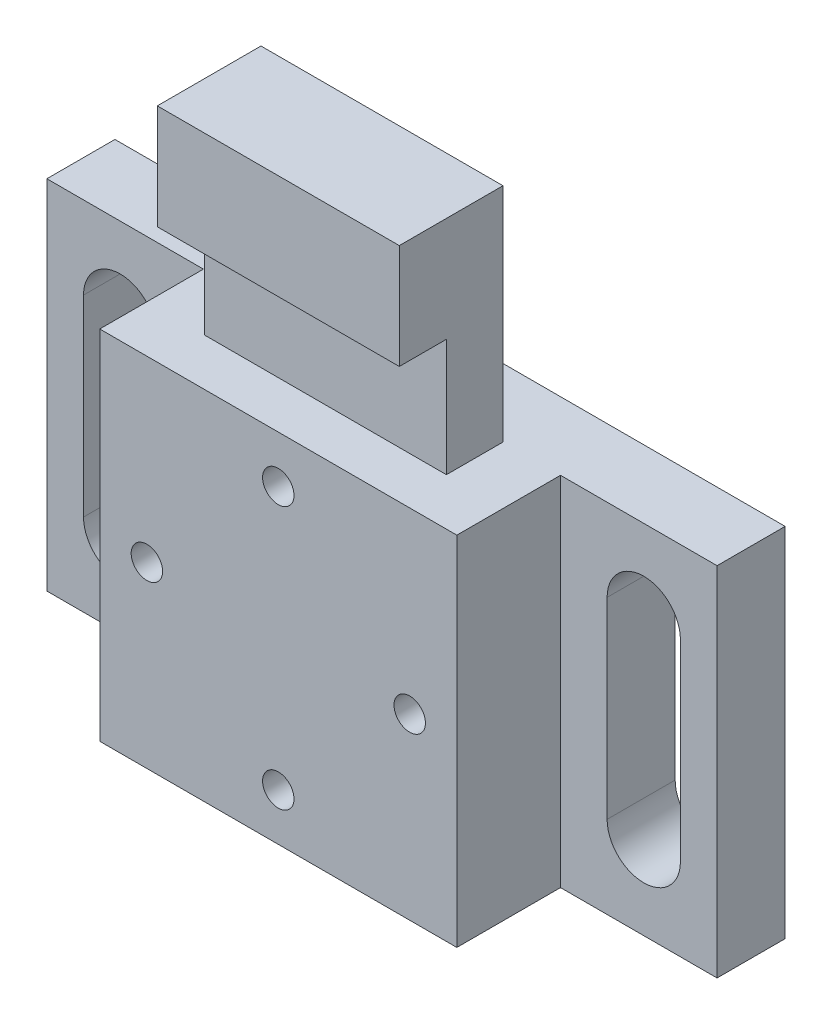
SolidWorks part; units mm, degrees
ref_plane "Front Plane" through (0, 0, 0) normal (0, 0, 1) x (1, 0, 0)
ref_plane "Top Plane" through (0, 0, 0) normal (0, 1, 0) x (1, 0, 0)
ref_plane "Right Plane" through (0, 0, 0) normal (1, 0, 0) x (0, 0, -1)
sketch "Sketch1" plane through (0, 0, 0) normal (0, 0, 1) x (1, 0, 0)
  line L1 (-32, 17.05) -> (32, 17.05)
  line L2 (-32, 17.05) -> (-32, -17.05)
  line L3 (-32, -17.05) -> (32, -17.05)
  line L4 (32, 17.05) -> (32, -17.05)
  point P4 (0, 17.05)
  point P5 (32, 0)
  dimension "D1" = 64
  dimension "D2" = 34.1
extrude "Boss-Extrude1" add sketch "Sketch1" along normal blind 6.5
sketch "Sketch2" plane through (0, 0, 6.5) normal (0, 0, 1) x (1, 0, 0)
  line L0 (32, 17.05) -> (-32, 17.05) construction
  line L1 (-17.05, 17.05) -> (-11.555, 17.05)
  line L2 (-17.05, 17.05) -> (-17.05, -17.05)
  line L3 (-17.05, -17.05) -> (17.05, -17.05)
  line L4 (17.05, 17.05) -> (17.05, -17.05)
  line L5 (-32, -17.05) -> (32, -17.05) construction
  line L7 (-11.555, 17.05) -> (-11.555, 38.25)
  line L8 (-11.555, 38.25) -> (11.555, 38.25)
  line L9 (11.555, 17.05) -> (11.555, 38.25)
  line L10 (11.555, 17.05) -> (17.05, 17.05)
  point P14 (0, 38.25)
  dimension "D1" = 34.1
  dimension "D2" = 55.3
  dimension "D3" = 23.11
extrude "Boss-Extrude2" add sketch "Sketch2" along normal blind 9.9
sketch "Sketch4" plane through (0, 0, 16.4) normal (0, 0, 1) x (1, 0, 0)
  line L0 (11.555, 17.05) -> (11.555, 38.25) construction
  line L1 (-11.555, 17.05) -> (11.555, 17.05)
  line L2 (-11.555, 17.05) -> (-11.555, 28.25)
  line L3 (-11.555, 28.25) -> (11.555, 28.25)
  line L4 (11.555, 17.05) -> (11.555, 28.25)
  line L5 (11.555, 38.25) -> (-11.555, 38.25) construction
  dimension "D1" = 10
extrude "Cut-Extrude1" cut sketch "Sketch4" against normal blind 4.5
ref_plane "Plane1" through (0, 0, 6.5) normal (0, 0, 1) x (1, 0, 0)
sketch "Sketch6" plane through (0, 0, 6.5) normal (0, 0, 1) x (1, 0, 0)
  line L1 (-25, 9.1787) -> (-25, -9.1787) construction
  line L2 (-21.5, 9.1787) -> (-21.5, -9.1787)
  line L3 (-28.5, 9.1787) -> (-28.5, -9.1787)
  line L4 (-32, 17.05) -> (-32, -17.05) construction
  arc A0 (-21.5, 9.1787) -> (-28.5, 9.1787) centre (-25, 9.1787) ccw
  arc A1 (-28.5, -9.1787) -> (-21.5, -9.1787) centre (-25, -9.1787) ccw
  point P5 (-25, 0)
  point P13 (-32, 0)
  dimension "D1" = 3.5
  dimension "D3" = 18.3574
  dimension "D2" = 7
extrude "Cut-Extrude2" cut sketch "Sketch6" against normal through all
mirror "Mirror1" about plane through (0, 0, 0) normal (1, 0, 0) of "Cut-Extrude2"
sketch "Sketch7" plane through (0, 0, 16.4) normal (0, 0, 1) x (1, 0, 0)
  line L0 (-24.8624, 0) -> (25.543, 0) construction
  line L1 (0, 21.1484) -> (0, -21.1812) construction
  line L3 (-17.05, -17.05) -> (17.05, -17.05) construction
  line L4 (-17.05, 17.05) -> (-17.05, -17.05) construction
  line L10 (17.05, 17.05) -> (-17.05, 17.05) construction
  circle A0 centre (-12.55, 0) radius 1.5
  circle A1 centre (12.55, 0) radius 1.5
  circle A2 centre (0, 12.55) radius 1.5
  circle A3 centre (0, -12.55) radius 1.5
  dimension "D1" = 3
  dimension "D2" = 3
  dimension "D3" = 3
  dimension "D4" = 3
  dimension "D5" = 3
extrude "Cut-Extrude3" cut sketch "Sketch7" against normal blind 10 contours A0 | A1 | A3 | A2
